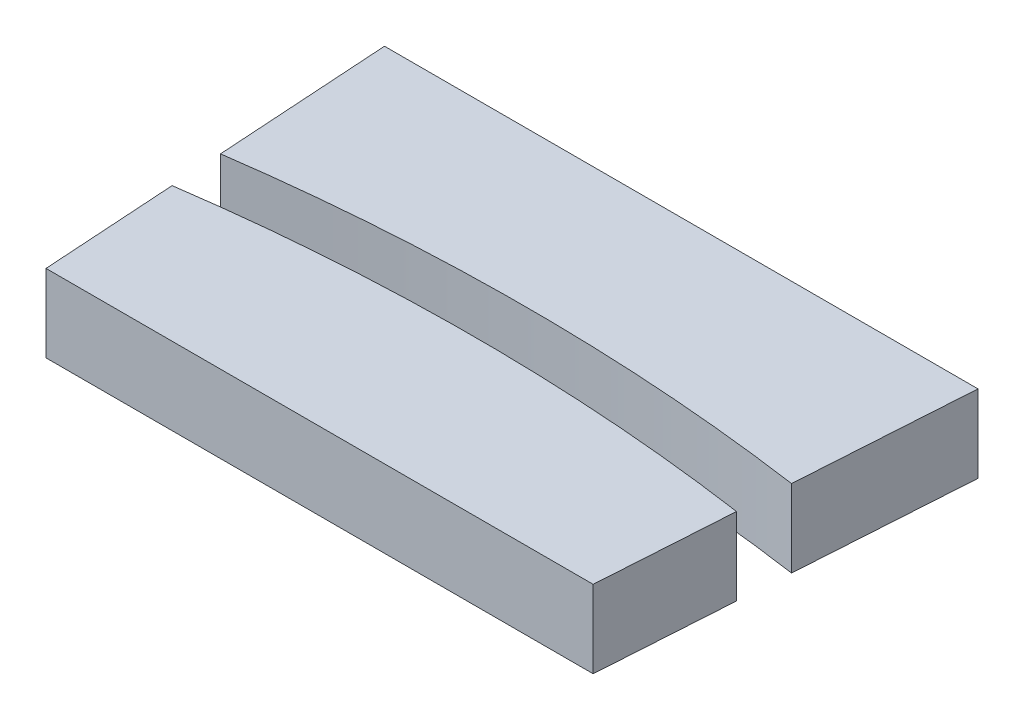
SolidWorks part; units mm, degrees
ref_plane "Front Plane" through (0, 0, 0) normal (0, 0, 1) x (1, 0, 0)
ref_plane "Top Plane" through (0, 0, 0) normal (0, 1, 0) x (1, 0, 0)
ref_plane "Right Plane" through (0, 0, 0) normal (1, 0, 0) x (0, 0, -1)
sketch "Sketch1" plane through (0, 0, 0) normal (0, 1, 0) x (1, 0, 0)
  line L0 (-12, 92.5) -> (0, 92.5)
  line L2 (0, 62.5) -> (-10.0775, 62.5)
  line L3 (-10.0775, 62.5) -> (-12, 92.5)
  line L4 (0, 92.5) -> (0, 62.5)
  point P2 (0, 77.5)
  dimension "D1" = 30
  dimension "D2" = 77.5
  dimension "D3" = 3.667
  dimension "D4" = 12
extrude "Boss-Extrude1" add sketch "Sketch1" along normal blind 3
mirror "Mirror1" about plane through (0, 0, 0) normal (1, 0, 0) of "Boss-Extrude1"
sketch "Sketch6" plane through (0, 3, 0) normal (0, 1, 0) x (1, 0, 0)
  line L1 (-12, 92.5) -> (-10.0775, 62.5) construction
  line L2 (-12, 92.5) -> (-10.0775, 62.5) construction
  line L3 (-10.5902, 70.5) -> (10.5902, 70.5)
  line L4 (12, 92.5) -> (10.0775, 62.5) construction
  line L6 (12, 92.5) -> (10.0775, 62.5) construction
  line L7 (11.4873, 84.5) -> (-11.4873, 84.5)
  line L8 (-10.0775, 62.5) -> (10.0775, 62.5) construction
  line L9 (-11.4873, 84.5) -> (-12, 92.5)
  line L10 (-12, 92.5) -> (12, 92.5)
  line L11 (12, 92.5) -> (11.4873, 84.5)
  line L12 (10.5902, 70.5) -> (10.0775, 62.5)
  line L13 (10.0775, 62.5) -> (-10.0775, 62.5)
  line L14 (-10.0775, 62.5) -> (-10.5902, 70.5)
  dimension "D1" = 14
  dimension "D2" = 8
extrude "Cut-Extrude4" cut sketch "Sketch6" against normal through all both and the other way through all
sketch "Sketch7" plane through (0, 3, 0) normal (0, 1, 0) x (1, 0, 0)
  line L0 (-11.4873, 84.5) -> (-10.5902, 70.5) construction
  line L1 (11.4873, 84.5) -> (10.5902, 70.5) construction
  line L2 (-11.1985, 77.6971) -> (-10.9244, 75.716)
  line L3 (10.9244, 75.716) -> (11.0527, 77.718)
  arc A0 (-11.1985, 77.6971) -> (11.0527, 77.718) centre (0, 0) cw
  arc A1 (-10.9244, 75.716) -> (10.9244, 75.716) centre (0, 0) cw
  dimension "D1" = 78.5
  dimension "D2" = 76.5
extrude "Cut-Extrude5" cut sketch "Sketch7" against normal through all both and the other way through all
